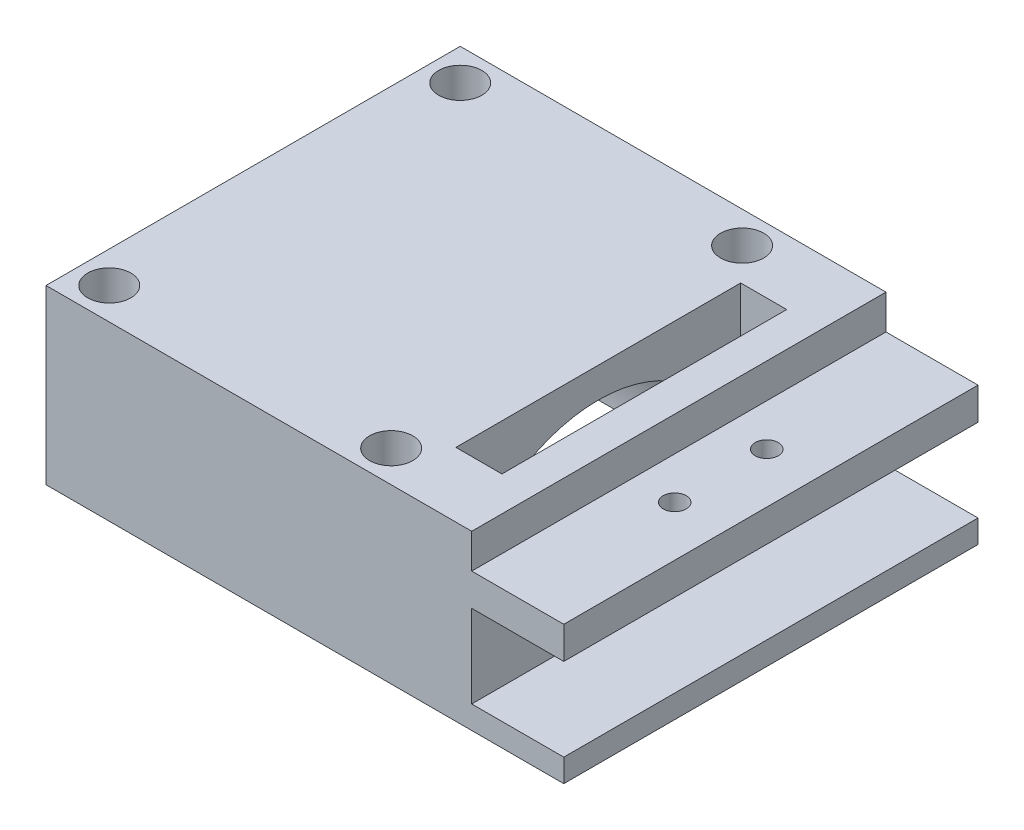
SolidWorks part; units mm, degrees
ref_plane "Front Plane" through (0, 0, 0) normal (0, 0, 1) x (1, 0, 0)
ref_plane "Top Plane" through (0, 0, 0) normal (0, 1, 0) x (1, 0, 0)
ref_plane "Right Plane" through (0, 0, 0) normal (1, 0, 0) x (0, 0, -1)
sketch "Sketch1" plane through (0, 0, 0) normal (0, 1, 0) x (1, 0, 0)
  line L1 (-15, -18) -> (15, -18)
  line L2 (-15, -18) -> (-15, 18)
  line L3 (-15, 18) -> (15, 18)
  line L4 (15, -18) -> (15, 18)
  line L5 (-15, -18) -> (15, 18) construction
  line L6 (-15, 18) -> (15, -18) construction
  point P0 (0, 0)
  dimension "D1" = 30
  dimension "D2" = 36
extrude "Boss-Extrude1" add sketch "Sketch1" along normal blind 30
sketch "Sketch3" plane through (15, 0, 0) normal (1, 0, 0) x (0, 0, -1)
  line L0 (0, 0) -> (0, 30) construction
  line L1 (-18, 0) -> (18, 0) construction
  line L2 (-18, 30) -> (18, 30) construction
  circle A0 centre (0, 15) radius 12.375
  dimension "D1" = 24.75
extrude "Cut-Extrude1" cut sketch "Sketch3" against normal blind 40
sketch "Sketch5" plane through (0, 30, 0) normal (0, 1, 0) x (1, 0, 0)
  line L7 (15, 18) -> (-15, 18) construction
  line L9 (-15, 18) -> (-15, -18) construction
  line L10 (0, 0) -> (0, 2.7791) construction
  line L11 (0, 2.7791) -> (0, 0) construction
  line L12 (0, 0) -> (-2.7536, 0) construction
  circle A1 centre (-12.25, 15.25) radius 1.875
  circle A2 centre (-12.25, -15.25) radius 1.875
  circle A3 centre (12.25, -15.25) radius 1.875
  circle A4 centre (12.25, 15.25) radius 1.875
  point P0 (0, 0)
  dimension "D2" = 3.75
  dimension "D3" = 2.75
  dimension "D4" = 2.75
extrude "Cut-Extrude2" cut sketch "Sketch5" against normal blind 40
sketch "Sketch7" plane through (0, 0, 0) normal (1, 0, 0) x (0, 0, -1)
  line L0 (-18, 30) -> (-18, 0) construction
  line L1 (-18, 15) -> (18, 15)
  line L2 (-18, 15) -> (-18, 0)
  line L3 (-18, 0) -> (18, 0)
  line L4 (18, 15) -> (18, 0)
extrude "Cut-Extrude3" cut sketch "Sketch7" against normal through all from surface at 15 starting at face at (15, 15, -12.375)
sketch "Sketch8" plane through (15, 0, 0) normal (1, 0, 0) x (0, 0, -1)
  line L0 (-12.375, 15) -> (-18, 15) construction
  line L1 (-18, 30) -> (-12.375, 30)
  line L2 (-18, 30) -> (-18, 15)
  line L3 (-18, 15) -> (-12.375, 15)
  line L4 (-12.375, 30) -> (-12.375, 15)
  line L6 (12.375, 15) -> (18, 15)
  line L7 (12.375, 15) -> (12.375, 30)
  line L8 (12.375, 30) -> (18, 30)
  line L9 (18, 15) -> (18, 30)
extrude "Boss-Extrude2" add sketch "Sketch8" along normal blind 7
sketch "Sketch10" plane through (22, 0, 0) normal (1, 0, 0) x (0, 0, -1)
  line L0 (12.375, 15) -> (18, 15) construction
  line L1 (-12.375, 30) -> (12.375, 30)
  line L2 (-12.375, 30) -> (-12.375, 15)
  line L3 (-12.375, 15) -> (12.375, 15)
  line L4 (12.375, 30) -> (12.375, 15)
extrude "Boss-Extrude3" add sketch "Sketch10" against normal blind 3
sketch "Sketch11" plane through (22, 0, 0) normal (1, 0, 0) x (0, 0, -1)
  line L0 (18, 15) -> (18, 30) construction
  line L1 (-18, 30) -> (18, 30)
  line L2 (-18, 30) -> (-18, 24.2)
  line L3 (-18, 24.2) -> (18, 24.2)
  line L4 (18, 30) -> (18, 24.2)
  line L5 (-18, 30) -> (-18, 15) construction
  line L6 (18, 15) -> (-18, 15)
  line L7 (18, 15) -> (18, 17)
  line L8 (18, 17) -> (-18, 17)
  line L9 (-18, 15) -> (-18, 17)
  line L10 (12.3151, 17) -> (12.3151, 24.2) construction
  dimension "D1" = 7.2
  dimension "D2" = 2
extrude "Boss-Extrude4" add sketch "Sketch11" along normal blind 8
sketch "Sketch12" plane through (0, 30, 0) normal (0, 1, 0) x (1, 0, 0)
  line L0 (-15, -18) -> (30, -18) construction
  line L1 (30, 18) -> (22, 18)
  line L2 (30, 18) -> (30, -18)
  line L3 (30, -18) -> (22, -18)
  line L4 (22, 18) -> (22, -18)
  dimension "D1" = 8
extrude "Cut-Extrude4" cut sketch "Sketch12" against normal blind 3
sketch "Sketch13" plane through (0, 27, 0) normal (0, 1, 0) x (1, 0, 0)
  line L3 (22, 18) -> (22, -18) construction
  line L6 (22, 0) -> (24.64, 0) construction
  line L7 (22, 18) -> (22, -18) construction
  circle A0 centre (25.64, 4) radius 1
  circle A1 centre (25.64, -4) radius 1
  dimension "D1" = 2
  dimension "D2" = 2
  dimension "D3" = 3.64
  dimension "D4" = 2.64
  dimension "D5" = 3.64
extrude "Cut-Extrude5" cut sketch "Sketch13" against normal blind 3
